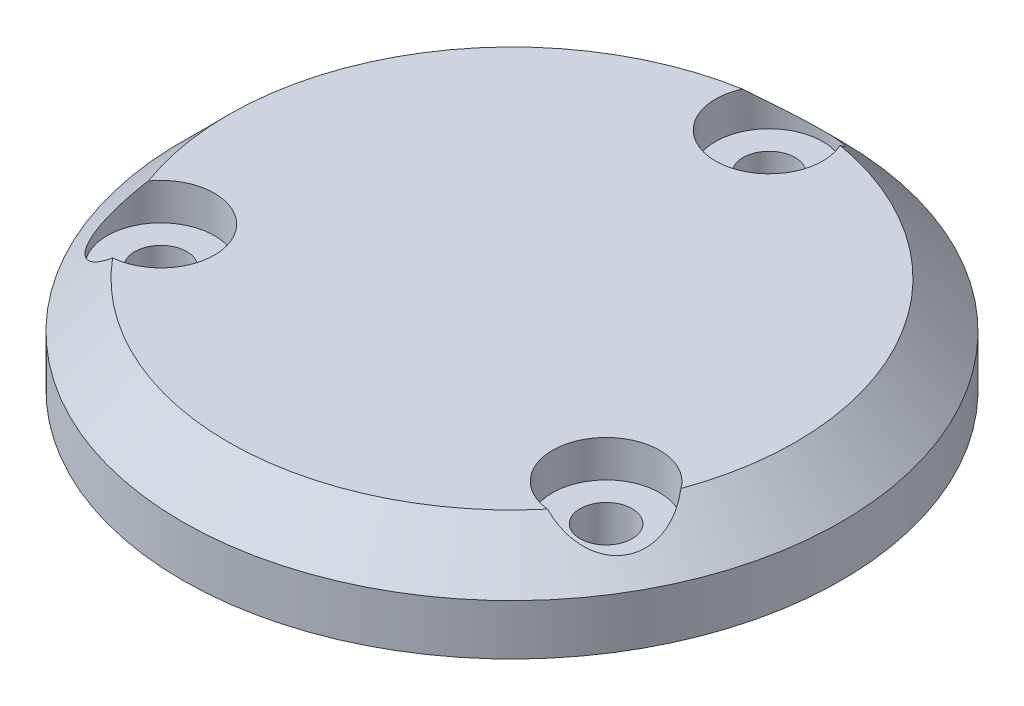
SolidWorks part; units mm, degrees
ref_plane "Płaszczyzna przednia" through (0, 0, 0) normal (0, 0, 1) x (1, 0, 0)
ref_plane "Płaszczyzna górna" through (0, 0, 0) normal (0, 1, 0) x (1, 0, 0)
ref_plane "Płaszczyzna prawa" through (0, 0, 0) normal (1, 0, 0) x (0, 0, -1)
sketch "Szkic2" plane through (0, 0, 0) normal (0, 1, 0) x (1, 0, 0)
  circle A0 centre (0, 0) radius 21.5
  dimension "D1" = 43
extrude "Dodanie-wyciągnięcie1" add sketch "Szkic2" against normal blind 3.3 and the other way blind 3 draft 45
hole_wizard "Pogłębienie walcowe pod M3 wkręt do części metalowych z łbem stożkowym ściętym2" positions "Szkic5" profile "Szkic6" counterbore size "M3" standard "Ansi Metric" end condition through all
sketch "Szkic5" plane through (0, 3, 0) normal (0, 1, 0) x (1, 0, 0)
  point P0 (0, 16.7721)
sketch "Szkic6" plane through (0, 3, -16.7721) normal (1, 0, 0) x (0, 0, 1)
  line L0 (0, 0) -> (0, 6.3)
  line L1 (0, 6.3) -> (1.7, 6.3)
  line L3 (1.7, 6.3) -> (1.7, 2.4)
  line L4 (1.7, 2.4) -> (3.5, 2.4)
  line L5 (3.5, 2.4) -> (3.5, 0)
  line L7 (3.5, 0) -> (0, 0)
  line L11 (0, -6.35) -> (0, 107.95) construction
  dimension "Średnica otworu na wylot" = 3.4
  dimension "Głębokość otworu na wylot" = 6.3
  dimension "Średnica pogłębienia walcowego" = 7
  dimension "Głębokość pogłębienia walcowego" = 2.4
pattern_circular "Szyk kołowy1" count 3 every 120 about axis through (0, 0, 0) along (0, 1, 0) of "Pogłębienie walcowe pod M3 wkręt do części metalowych z łbem stożkowym ściętym2"
